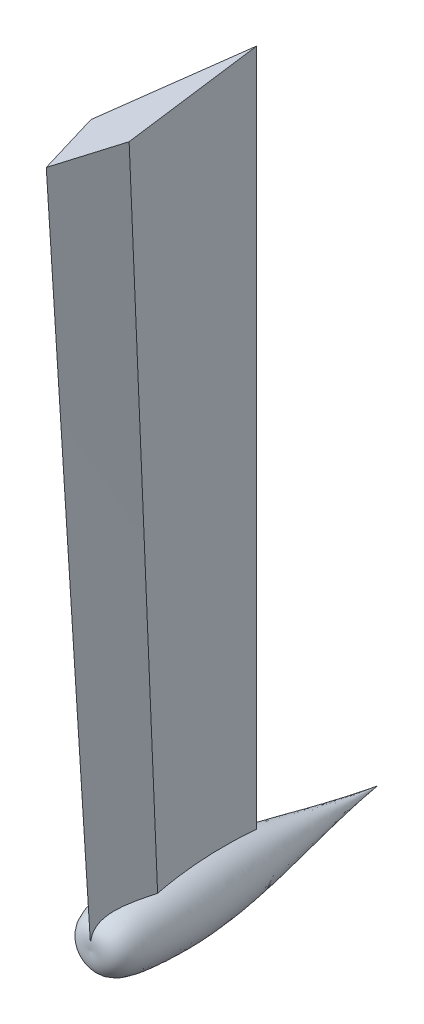
SolidWorks part; units mm, degrees
ref_plane "Front Plane" through (0, 0, 0) normal (0, 0, 1) x (1, 0, 0)
ref_plane "Top Plane" through (0, 0, 0) normal (0, 1, 0) x (1, 0, 0)
ref_plane "Right Plane" through (0, 0, 0) normal (1, 0, 0) x (0, 0, -1)
sketch "Sketch1" plane through (0, 0, 0) normal (0, 1, 0) x (1, 0, 0)
  line L0 (0, 0) -> (0, -330) construction
  line L1 (0, -330) -> (30, -230)
  line L2 (30, -230) -> (0, 0)
  line L3 (0, 0) -> (-30, -230)
  line L4 (-30, -230) -> (0, -330)
  line L5 (-30, -230) -> (30, -230) construction
  point P2 (0, 0)
  point P6 (0, -230)
  point P7 (0, 0)
  point P9 (0.5544, -319.89)
  dimension "D1" = 330
  dimension "D2" = 60
  dimension "D3" = 100
sketch3d "3DSketch1" plane through (0, 0, 0) normal (0, 0, 1) x (1, 0, 0)
  dimension "D1" = 1100
sketch "Sketch2" plane through (0, -1100, 0) normal (0, 1, 0) x (1, 0, 0)
  line L0 (0, 0) -> (0, -260) construction
  line L1 (0, 0) -> (20, -173.3333)
  line L2 (20, -173.3333) -> (0, -260)
  line L3 (0, -260) -> (-20, -173.3333)
  line L4 (-20, -173.3333) -> (0, 0)
  line L5 (20, -173.3333) -> (-20, -173.3333) construction
  point P3 (0, -173.3333)
  dimension "D1" = 260
  dimension "D2" = 40
  dimension "D3" = 86.6667
loft "Loft1" add profiles "Sketch1", "Sketch2"
sketch "Sketch5" plane through (0, -1100, 0) normal (0, 1, 0) x (1, 0, 0)
  line L0 (0, 0) -> (0, -260) construction
  line L1 (0, -260) -> (0, 190) construction
  line L2 (0, -260) -> (0, 190)
  spline S1 degree 3 poles (0, -260) (41.0128, -265.6506) (71.9998, -83.7287) (18.7033, 55.4773) (0, 190) knots 0 0 0 0 0.181249 1 1 1 1
  point P5 (32.995, -6.1417)
  point P6 (0, 0)
  point P7 (23.059, 0)
  point P9 (35.7289, -249.2128)
  point P11 (63.2266, -205.9549)
  point P12 (41.0779, 2.213)
  point P13 (0, 0)
  point P15 (39.8184, 13.0784)
  point P16 (25.6524, 52.5427)
  point P17 (49.4767, -201.1075)
  dimension "D1" = 450
revolve "Revolve1" add sketch "Sketch5" angle 360 about L2
